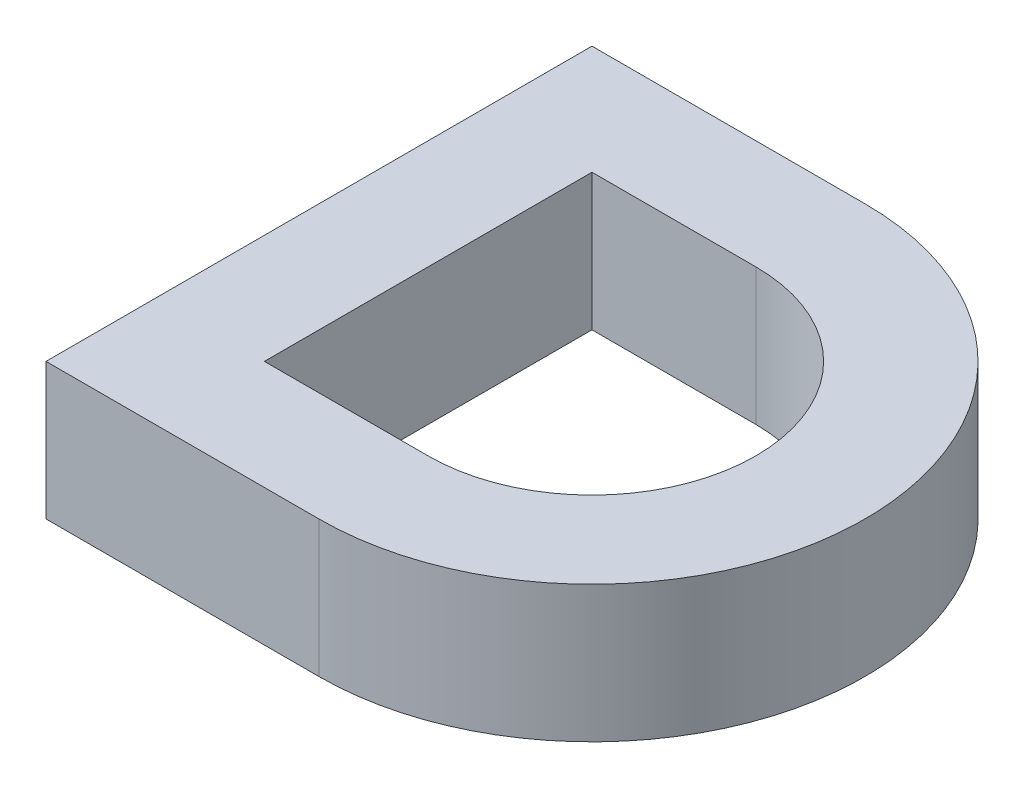
SolidWorks part; units mm, degrees
ref_plane "Front Plane" through (0, 0, 0) normal (0, 0, 1) x (1, 0, 0)
ref_plane "Top Plane" through (0, 0, 0) normal (0, 1, 0) x (1, 0, 0)
ref_plane "Right Plane" through (0, 0, 0) normal (1, 0, 0) x (0, 0, -1)
sketch "Sketch1" plane through (0, 0, 0) normal (0, 1, 0) x (1, 0, 0)
  line L0 (150, 0) -> (150, 40)
  line L1 (150, 40) -> (170, 40)
  line L2 (170, 0) -> (150, 0)
  line L3 (170, 32) -> (158, 32)
  line L4 (158, 32) -> (158, 8)
  line L5 (158, 8) -> (170, 8)
  arc A0 (170, 40) -> (170, 0) centre (170, 20) cw
  arc A1 (170, 8) -> (170, 32) centre (170, 20) ccw
  point P11 (0, 0)
  point P12 (0, 0)
  dimension "D1" = 150
  dimension "D2" = 40
  dimension "D3" = 40
  dimension "D5" = 8
  dimension "D6" = 8
extrude "Boss-Extrude1" add sketch "Sketch1" along normal blind 10
